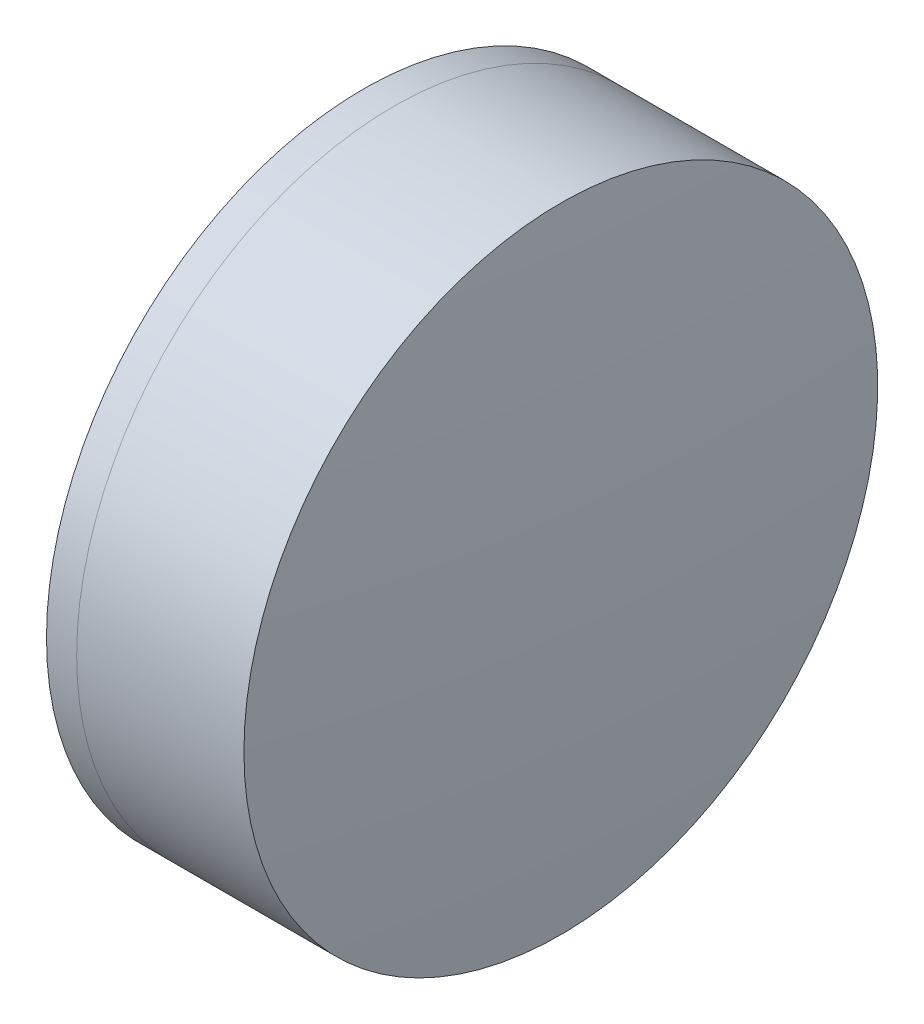
SolidWorks part; units mm, degrees
ref_plane "前视基准面" through (0, 0, 0) normal (0, 0, 1) x (1, 0, 0)
ref_plane "上视基准面" through (0, 0, 0) normal (0, 1, 0) x (1, 0, 0)
ref_plane "右视基准面" through (0, 0, 0) normal (1, 0, 0) x (0, 0, -1)
sketch "草图1" plane through (0, 0, 0) normal (0, 1, 0) x (1, 0, 0)
  line L0 (124.5233, 0) -> (646.9917, 0) construction
  line L1 (268.5918, -6.35) -> (269.1964, -6.35)
  line L2 (268.5918, 6.35) -> (269.1964, 6.35)
  arc A0 (269.1964, -6.35) -> (269.1964, 6.35) centre (260.709, 0) ccw
  arc A1 (268.5918, 6.35) -> (268.5918, -6.35) centre (279.009, 0) ccw
  point P10 (266.809, 0)
  point P11 (271.309, 0)
  dimension "D3" = 12.2
  dimension "D4" = 10.6
  dimension "D1" = 6.35
  dimension "D2" = 6.35
  dimension "D5" = 4.5
revolve "旋转1" add sketch "草图1" angle 360 about L0
sketch "草图2" plane through (0, 0, 0) normal (0, 1, 0) x (1, 0, 0)
  line L0 (-0.5519, 0) -> (622.6607, 0) construction
  line L2 (269.1964, 6.35) -> (272.548, 6.35)
  line L3 (269.1964, -6.35) -> (272.548, -6.35)
  arc A0 (272.548, -6.35) -> (272.548, 6.35) centre (195.409, 0) ccw
  arc A1 (269.1964, -6.35) -> (269.1964, 6.35) centre (260.709, 0) ccw construction
  arc A2 (269.1964, -6.35) -> (269.1964, 6.35) centre (260.709, 0) ccw
  point P4 (271.309, 0)
  point P8 (272.809, 0)
  dimension "D1" = 77.4
  dimension "D2" = 1.5
revolve "旋转3" add sketch "草图2" angle 360 about L0
